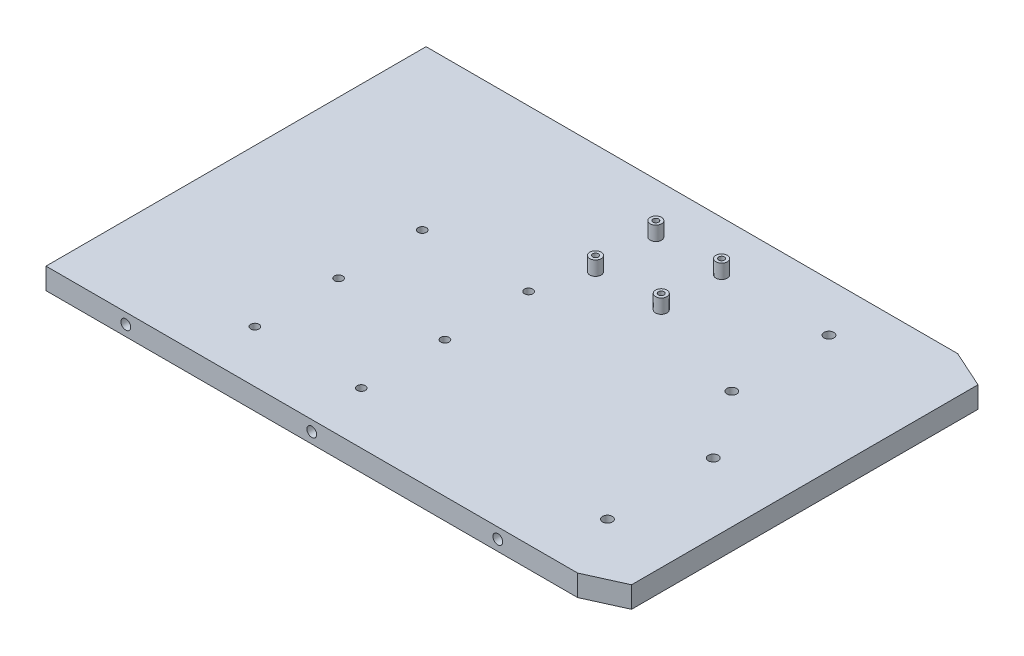
SolidWorks part; units mm, degrees
ref_plane "Front Plane" through (0, 0, 0) normal (0, 0, 1) x (1, 0, 0)
ref_plane "Top Plane" through (0, 0, 0) normal (0, 1, 0) x (1, 0, 0)
ref_plane "Right Plane" through (0, 0, 0) normal (1, 0, 0) x (0, 0, -1)
sketch "Sketch1" plane through (0, 0, 0) normal (0, 1, 0) x (1, 0, 0)
  line L2 (0, 12.0331) -> (0, 268.5969)
  line L6 (374.81, 274.2969) -> (374.81, 268.5969)
  line L9 (401.01, 18.185) -> (401.01, 262.445)
  line L10 (401.01, 262.445) -> (374.81, 274.2969)
  line L12 (374.81, 268.5969) -> (0, 268.5969)
  line L13 (0, 140.315) -> (401.01, 140.315) construction
  line L15 (401.01, 18.185) -> (374.81, 6.3331)
  line L17 (374.81, 12.0331) -> (0, 12.0331)
  line L18 (374.81, 6.3331) -> (374.81, 12.0331)
extrude "Boss-Extrude1" add sketch "Sketch1" along normal blind 10
sketch "Sketch2" plane through (0, 10, 0) normal (0, 1, 0) x (1, 0, 0)
  line L0 (0, 268.5969) -> (0, 12.0331)
  line L1 (352.4341, 121.6803) -> (352.4341, 127.0803) construction
  line L2 (0, 12.0331) -> (374.81, 12.0331)
  line L3 (352.4341, 52.4303) -> (352.4341, 47.0303) construction
  line L4 (374.81, 12.0331) -> (374.81, 6.3331)
  line L5 (374.81, 6.3331) -> (401.01, 18.185)
  line L6 (401.01, 18.185) -> (401.01, 262.445)
  line L7 (401.01, 262.445) -> (374.81, 274.2969)
  line L8 (374.81, 274.2969) -> (374.81, 268.5969)
  line L9 (374.81, 268.5969) -> (0, 268.5969)
  circle A0 centre (185.5985, 102.0168) radius 2.925
  circle A1 centre (185.5985, 161.0168) radius 2.925
  circle A2 centre (185.5985, 43.0168) radius 2.925
  circle A3 centre (110.5985, 43.0168) radius 2.925
  circle A4 centre (110.5985, 102.0168) radius 2.925
  circle A5 centre (110.5985, 161.0168) radius 2.925
  circle A8 centre (352.4341, 124.3803) radius 3.455
  circle A9 centre (352.4341, 49.7303) radius 3.455
  circle A10 centre (318.1841, 240.1847) radius 3.45
  circle A11 centre (318.1841, 171.6847) radius 3.45
  point P1 (0, 0)
extrude "Boss-Extrude3" add sketch "Sketch2" along normal blind 5
sketch "Sketch3" plane through (0, 15, 0) normal (0, 1, 0) x (1, 0, 0)
  circle A0 centre (197.1863, 196.582) radius 2
  circle A1 centre (243.5413, 196.582) radius 2
  circle A2 centre (243.5413, 239.127) radius 2
  circle A3 centre (197.1863, 239.127) radius 2
  circle A4 centre (197.1863, 196.582) radius 4
  circle A5 centre (197.1863, 239.127) radius 4
  circle A6 centre (243.5413, 239.127) radius 4
  circle A8 centre (243.5413, 196.582) radius 4
extrude "Boss-Extrude4" add sketch "Sketch3" along normal blind 10
sketch "Sketch4" plane through (0, 0, -12.0331) normal (0, 0, 1) x (1, 0, 0)
  line L1 (0, 0) -> (374.81, 0)
  line L2 (0, 0) -> (0, 15)
  line L3 (0, 15) -> (374.81, 15)
  line L4 (374.81, 0) -> (374.81, 15)
  circle A0 centre (187.405, 7.5) radius 3.455
  circle A1 centre (56.2694, 7.5) radius 3.455
  circle A2 centre (318.5406, 7.5) radius 3.455
extrude "Boss-Extrude5" add sketch "Sketch4" along normal blind 5.7
sketch "Sketch5" plane through (0, 0, -268.5969) normal (0, 0, -1) x (-1, 0, 0)
  line L0 (-374.81, 0) -> (0, 0)
  line L1 (-374.81, 0) -> (-374.81, 15)
  line L2 (-374.81, 15) -> (0, 15)
  line L3 (0, 0) -> (0, 15)
  line L4 (-374.81, 15) -> (-374.81, 0) construction
  line L5 (-374.81, 15) -> (-374.81, 0) construction
  circle A0 centre (-187.405, 7.5) radius 3.455
  circle A1 centre (-318.5406, 7.5) radius 3.455
  circle A2 centre (-56.2694, 7.5) radius 3.455
extrude "Boss-Extrude6" add sketch "Sketch5" along normal blind 5.7
